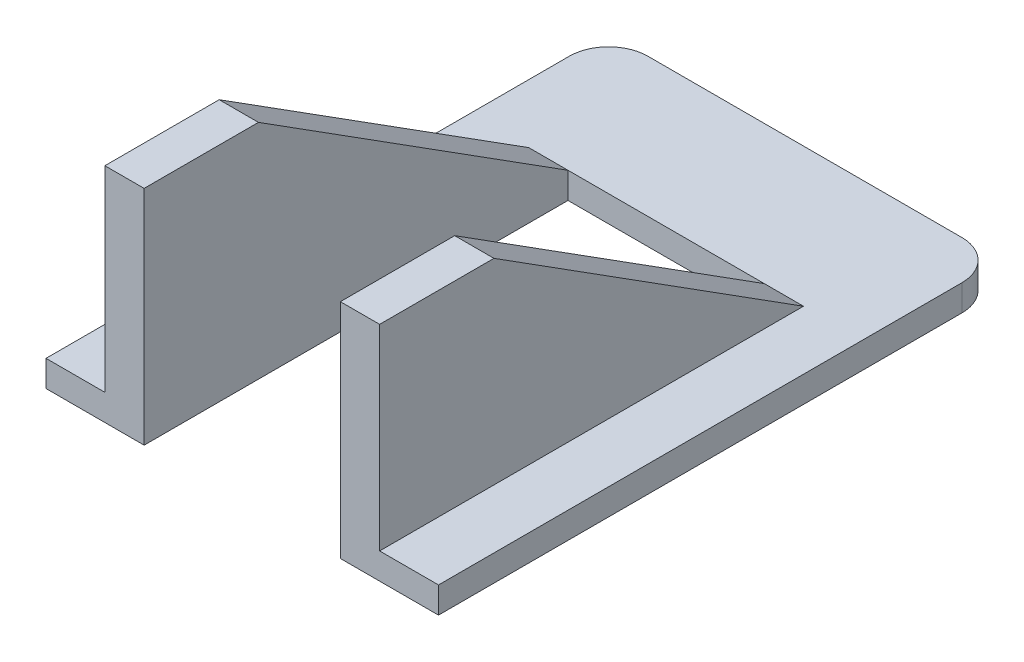
SolidWorks part; units mm, degrees
ref_plane "Alzado" through (0, 0, 0) normal (0, 0, 1) x (1, 0, 0)
ref_plane "Planta" through (0, 0, 0) normal (0, 1, 0) x (1, 0, 0)
ref_plane "Vista lateral" through (0, 0, 0) normal (1, 0, 0) x (0, 0, -1)
sketch "Croquis2" plane through (0, 0, 0) normal (1, 0, 0) x (0, 0, -1)
  line L1 (-41.2833, 1.4772) -> (1.7167, 1.4772)
  line L2 (-41.2833, 1.4772) -> (-41.2833, -28.5228)
  line L3 (-41.2833, -28.5228) -> (1.7167, -28.5228)
  line L4 (1.7167, 1.4772) -> (1.7167, -28.5228)
  dimension "D1" = 30
  dimension "D2" = 43
extrude "Saliente-Extruir1" add sketch "Croquis2" along normal blind 30
sketch "Croquis3" plane through (30, 0, 0) normal (1, 0, 0) x (0, 0, -1)
  line L0 (-41.2833, 1.4772) -> (-41.2833, -28.5228) construction
  line L1 (-38.2833, -44.0813) -> (4.2461, -44.0813)
  line L2 (-38.2833, -44.0813) -> (-38.2833, -18.5228)
  line L3 (-38.2833, -18.5228) -> (4.2461, -18.5228)
  line L4 (4.2461, -44.0813) -> (4.2461, -18.5228)
  line L5 (-41.2833, -28.5228) -> (1.7167, -28.5228) construction
  line L6 (-31.6751, 1.4772) -> (-3.2833, -16.5228)
  line L7 (1.7167, 1.4772) -> (-41.2833, 1.4772) construction
  line L8 (-3.2833, -16.5228) -> (1.7167, -16.5228)
  line L9 (1.7167, -28.5228) -> (1.7167, 1.4772) construction
  line L10 (1.7167, -16.5228) -> (1.7167, 1.4772)
  line L11 (1.7167, 1.4772) -> (-31.6751, 1.4772)
  dimension "D1" = 3
  dimension "D2" = 10
  dimension "D3" = 2
  dimension "D4" = 5
extrude "Cortar-Extruir1" cut sketch "Croquis3" against normal blind 30
sketch "Croquis4" plane through (30, 0, 0) normal (1, 0, 0) x (0, 0, -1)
  line L0 (-41.2833, -1.5228) -> (-32.5459, -1.5228)
  line L1 (-41.2833, 1.4772) -> (-41.2833, -28.5228) construction
  line L2 (-32.5459, -1.5228) -> (-8.8861, -16.5228)
  line L3 (-8.8861, -16.5228) -> (-41.2833, -16.5228)
  line L4 (-41.2833, -16.5228) -> (-41.2833, -1.5228)
  line L5 (-31.6751, 1.4772) -> (-41.2833, 1.4772) construction
  line L6 (1.7167, -18.5228) -> (-38.2833, -18.5228) construction
  line L7 (-31.6751, 1.4772) -> (-3.2833, -16.5228) construction
  dimension "D1" = 3
  dimension "D2" = 2
  dimension "D3" = 3
extrude "Cortar-Extruir2" cut sketch "Croquis4" against normal offset from surface (15 mm away) 7.5 from offset 7.5 up to face at (0, -15.5228, 23.8322) offset against normal yes
sketch "Croquis5" plane through (30, 0, 0) normal (1, 0, 0) x (0, 0, -1)
  line L1 (-3.2833, -16.5228) -> (-41.2833, -16.5228)
  line L8 (-38.2833, -28.5228) -> (-38.2833, -18.5228)
  line L9 (-38.2833, -18.5228) -> (1.7167, -18.5228)
  line L10 (1.7167, -18.5228) -> (1.7167, -16.5228)
  line L11 (1.7167, -16.5228) -> (-3.2833, -16.5228)
  line L12 (-3.2833, -16.5228) -> (-31.6751, 1.4772)
  line L13 (-31.6751, 1.4772) -> (-41.2833, 1.4772)
  line L14 (-41.2833, 1.4772) -> (-41.2833, -28.5228)
  line L15 (-41.2833, -28.5228) -> (-38.2833, -28.5228)
  line L20 (-3.2833, -16.5228) -> (-31.6751, 1.4772)
  line L21 (-31.6751, 1.4772) -> (-41.2833, 1.4772)
  line L22 (-41.2833, 1.4772) -> (-41.2833, -16.5228)
  dimension "D1" = 0
extrude "Cortar-Extruir4" cut sketch "Croquis5" against normal blind 4.5
sketch "Croquis6" plane through (0, 0, 0) normal (-1, 0, 0) x (0, 0, 1)
  line L0 (3.2833, -16.5228) -> (41.2833, -16.5228)
  line L8 (-1.7167, -18.5228) -> (38.2833, -18.5228)
  line L9 (38.2833, -18.5228) -> (38.2833, -28.5228)
  line L10 (38.2833, -28.5228) -> (41.2833, -28.5228)
  line L11 (41.2833, -28.5228) -> (41.2833, 1.4772)
  line L12 (41.2833, 1.4772) -> (31.6751, 1.4772)
  line L13 (31.6751, 1.4772) -> (3.2833, -16.5228)
  line L14 (3.2833, -16.5228) -> (-1.7167, -16.5228)
  line L15 (-1.7167, -16.5228) -> (-1.7167, -18.5228)
  line L19 (41.2833, -16.5228) -> (41.2833, 1.4772)
  line L20 (41.2833, 1.4772) -> (31.6751, 1.4772)
  line L21 (31.6751, 1.4772) -> (3.2833, -16.5228)
  dimension "D1" = 0
extrude "Cortar-Extruir5" cut sketch "Croquis6" against normal blind 4.5
fillet "Redondeo1" radius 3 2 edges at (30, -17.5228, -1.7167) (0, -17.5228, -1.7167)
sketch "Croquis8" plane through (0, -16.5228, 0) normal (0, 1, 0) x (1, 0, 0)
  line L4 (7.5, -8.8861) -> (7.5, -41.2833)
  line L5 (7.5, -41.2833) -> (22.5, -41.2833)
  line L6 (22.5, -41.2833) -> (22.5, -8.8861)
  line L7 (22.5, -8.8861) -> (7.5, -8.8861)
  line L8 (7.5, -8.8861) -> (7.5, -41.2833)
  line L9 (7.5, -41.2833) -> (22.5, -41.2833)
  line L10 (22.5, -41.2833) -> (22.5, -8.8861)
  line L11 (22.5, -8.8861) -> (7.5, -8.8861)
  dimension "D1" = 0
extrude "Cortar-Extruir6" cut sketch "Croquis8" against normal blind 4.5
sketch "Croquis9" plane through (0, -18.5228, 0) normal (0, -1, 0) x (1, 0, 0)
  line L1 (77.7572, 22.6846) -> (-42.526, 22.6846)
  line L2 (77.7572, 22.6846) -> (77.7572, 101.4947)
  line L3 (77.7572, 101.4947) -> (-42.526, 101.4947)
  line L4 (-42.526, 22.6846) -> (-42.526, 101.4947)
extrude "Cortar-Extruir7" cut sketch "Croquis9" along normal blind 22.5
sketch "Croquis10" plane through (25.5, 0, 0) normal (1, 0, 0) x (0, 0, -1)
  line L0 (-41.2833, -1.5228) -> (-32.5459, -1.5228)
  line L1 (-32.5459, -1.5228) -> (-8.8861, -16.5228)
  line L2 (-8.8861, -16.5228) -> (1.7167, -16.5228)
  line L3 (1.7167, -16.5228) -> (-27.7102, 4.9022)
  line L4 (-27.7102, 4.9022) -> (-44.2285, 5.2703)
  line L5 (-44.2285, 5.2703) -> (-41.2833, -1.5228)
extrude "Cortar-Extruir8" cut sketch "Croquis10" against normal blind 22.5
